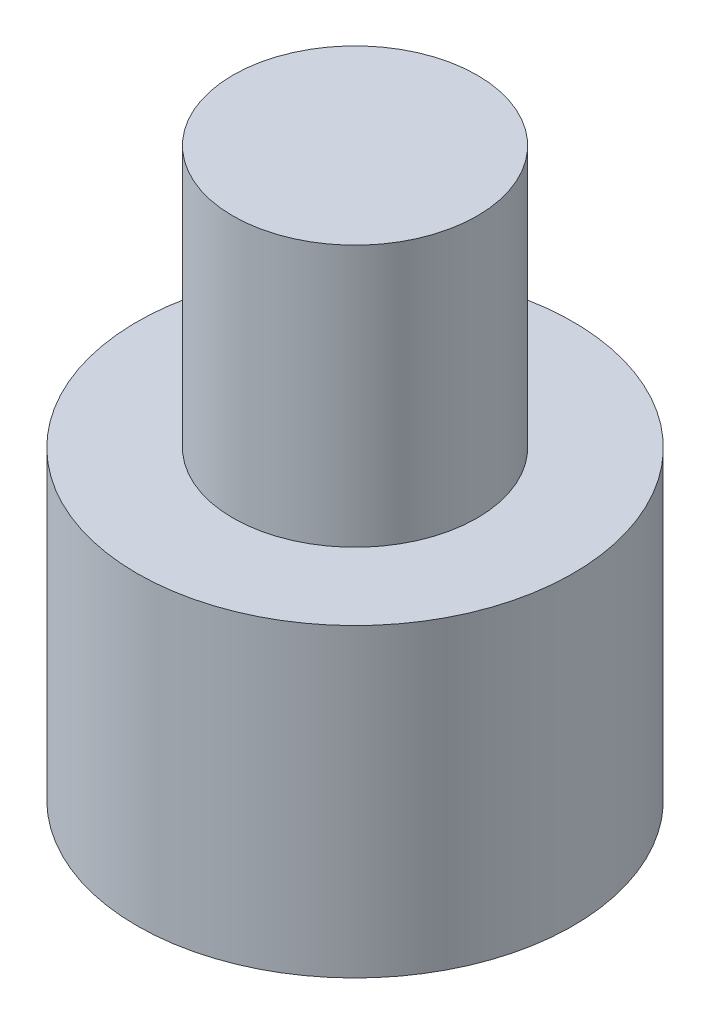
SolidWorks part; units mm, degrees
ref_plane "Plan de face" through (0, 0, 0) normal (0, 0, 1) x (1, 0, 0)
ref_plane "Plan de dessus" through (0, 0, 0) normal (0, 1, 0) x (1, 0, 0)
ref_plane "Plan de droite" through (0, 0, 0) normal (1, 0, 0) x (0, 0, -1)
sketch "Esquisse1" plane through (0, 0, 0) normal (0, 1, 0) x (1, 0, 0)
  circle A0 centre (0, 0) radius 1.4
  dimension "D1" = 2.8
extrude "Boss.-Extru.1" add sketch "Esquisse1" along normal blind 6.5
sketch "Esquisse2" plane through (0, 0, 0) normal (0, 1, 0) x (1, 0, 0)
  circle A0 centre (0, 0) radius 2.5
  dimension "D1" = 5
extrude "Boss.-Extru.2" add sketch "Esquisse2" along normal blind 3.5
